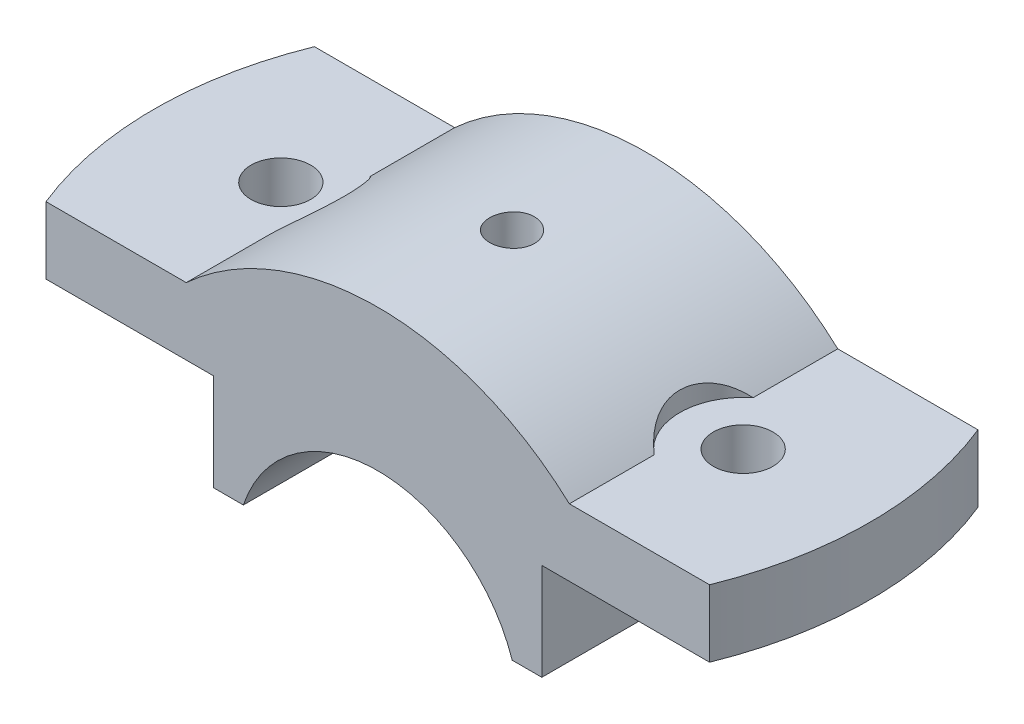
SolidWorks part; units mm, degrees
ref_plane "Front Plane" through (0, 0, 0) normal (0, 0, 1) x (1, 0, 0)
ref_plane "Top Plane" through (0, 0, 0) normal (0, 1, 0) x (1, 0, 0)
ref_plane "Right Plane" through (0, 0, 0) normal (1, 0, 0) x (0, 0, -1)
sketch "Sketch2" plane through (0, 0, 0) normal (0, 0, 1) x (1, 0, 0)
  line L0 (0, 0) -> (0, 40.9063) construction
  line L1 (18.0278, 0) -> (22, 0)
  line L2 (22, 0) -> (22, 13)
  line L3 (22, 13) -> (50, 13)
  line L4 (50, 13) -> (50, 22)
  line L5 (50, 22) -> (25.6905, 22)
  line L6 (-50, 22) -> (-25.6905, 22)
  line L7 (-50, 13) -> (-50, 22)
  line L8 (-22, 13) -> (-50, 13)
  line L9 (-22, 0) -> (-22, 13)
  line L10 (-18.0278, 0) -> (-22, 0)
  arc A0 (18.0278, 0) -> (-18.0278, 0) centre (0, -6) ccw
  arc A1 (25.6905, 22) -> (-25.6905, 22) centre (0, -6) ccw
  dimension "D6" = 19
  dimension "D7" = 38
  dimension "D1" = 44
  dimension "D2" = 0
  dimension "D3" = 13
  dimension "D4" = 6
  dimension "D5" = 9
  dimension "D8" = 100
extrude "Boss-Extrude1" add sketch "Sketch2" along normal mid plane 36
hole_wizard "Ø8.0mm Dowel Hole1" positions "Sketch6" profile "Sketch5" hole size "Ø8.0" standard "AS" end condition through all
sketch "Sketch6" plane through (0, 22, 0) normal (0, 1, 0) x (1, 0, 0)
  point P0 (-31, 0)
  dimension "D1" = 31
sketch "Sketch5" plane through (-31, 22, 0) normal (1, 0, 0) x (0, 0, 1)
  line L0 (0, 0) -> (0, 22)
  line L1 (0, 22) -> (4, 22)
  line L2 (4, 22) -> (4, 0)
  line L5 (4, 0) -> (0, 0)
  line L11 (0, -6.35) -> (0, 107.95) construction
  dimension "Thru Hole Dia." = 8
  dimension "Thru Hole Depth" = 22
sketch "Sketch9" plane through (0, 22, 0) normal (0, 1, 0) x (1, 0, 0)
  line L4 (-25.6905, 18) -> (-50, 18)
  line L5 (-50, 18) -> (-50, -18)
  line L6 (-50, -18) -> (-25.6905, -18)
  line L7 (-25.6905, -18) -> (-25.6905, 18)
  line L8 (-25.6905, 18) -> (-50, 18)
  line L9 (-50, 18) -> (-50, -18)
  line L10 (-50, -18) -> (-25.6905, -18)
  line L11 (-25.6905, -18) -> (-25.6905, 18)
  arc A0 (-44.4972, 18) -> (-44.4972, -18) centre (0, 0) ccw
  line M7 (-50, 18) -> (-50, -18)
  line M8 (-50, -18) -> (-25.6905, -18)
  dimension "D2" = 48
  dimension "D1" = 0
extrude "Cut-Extrude1" cut sketch "Sketch9" against normal blind 36 contours A0 L8 M7 M8
mirror "Mirror1" about plane through (0, 0, 0) normal (1, 0, 0) of "Ø8.0mm Dowel Hole1", "Cut-Extrude1"
hole_wizard "CBORE for M5 Hex Head Bolt1" positions "3DSketch2" profile "Sketch10" counterbore size "M5" standard "ANSI Metric" end condition through all
sketch3d "3DSketch2"
  point P0 (0, 0, 0)
  point P3 (0, 0, 0)
  point P5 (0, 0, 0)
  point P7 (0, 0, 0)
  point P9 (0, 0, 0)
  point P11 (0, 32, 0)
  dimension "D1" = 0
  dimension "D2" = 0
sketch "Sketch10" plane through (0, 32, 0) normal (1, 0, 0) x (0, 0, 1)
  line L0 (0, 0) -> (0, 32)
  line L1 (0, 32) -> (2.5, 32)
  line L2 (2.5, 13.495) -> (2.5, 32)
  line L3 (2.5, 13.495) -> (2.995, 13)
  line L4 (2.995, 13) -> (3, 13)
  line L5 (3, 13) -> (3, 0)
  line L7 (0, 0) -> (3, 0)
  line L9 (-2.5, 13.495) -> (-2.995, 13) construction
  line L11 (0, -6.35) -> (0, 107.95) construction
  dimension "Thru Hole Dia." = 5
  dimension "Thru Hole Depth" = 32
  dimension "C'Bore Dia." = 6
  dimension "C'Bore Depth" = 13
  dimension "Mid C'Sink Dia." = 5.99
  dimension "Mid C'Sink Angle" = 90
sketch "Sketch12" plane through (0, 22, 0) normal (0, 1, 0) x (1, 0, 0)
  line L0 (25.6905, 18) -> (-25.6905, 18) construction
  line L1 (25.6905, -18) -> (25.6905, 18) construction
  line L2 (-25.6905, -18) -> (25.6905, -18) construction
  line L3 (-44.4972, -18) -> (-25.6905, -18)
  line L4 (-25.6905, -18) -> (-25.6905, 18)
  line L5 (-25.6905, 18) -> (-44.4972, 18)
  line L6 (-44.4972, -18) -> (-25.6905, -18)
  line L7 (-25.6905, -18) -> (-25.6905, 18)
  line L8 (-25.6905, 18) -> (-44.4972, 18)
  line L9 (25.6905, 18) -> (-25.6905, 18)
  line L10 (25.6905, -18) -> (25.6905, 18)
  line L11 (-25.6905, -18) -> (25.6905, -18)
  arc A0 (-25.6905, -6.6377) -> (-25.6905, 6.6377) centre (-31, 0) ccw
  arc A1 (-44.4972, 18) -> (-44.4972, -18) centre (0, 0) ccw
  arc A2 (-44.4972, 18) -> (-44.4972, -18) centre (0, 0) ccw
  dimension "D2" = 8.5
  dimension "D1" = 0
extrude "Cut-Extrude4" cut sketch "Sketch12" along normal blind 36 contours L7 A0
mirror "Mirror2" about plane through (0, 0, 0) normal (1, 0, 0) of "Cut-Extrude4"
